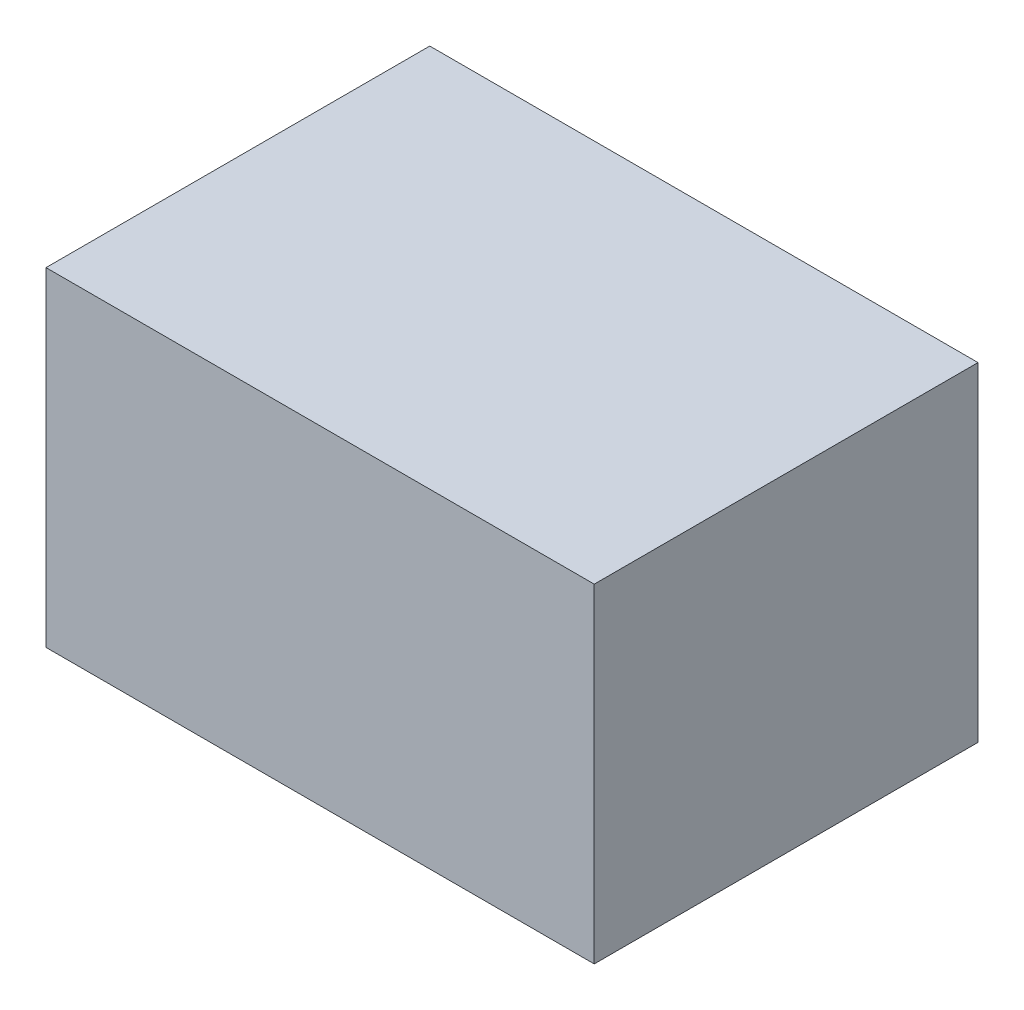
SolidWorks part; units mm, degrees
ref_plane "Спереди" through (0, 0, 0) normal (0, 0, 1) x (1, 0, 0)
ref_plane "Сверху" through (0, 0, 0) normal (0, 1, 0) x (1, 0, 0)
ref_plane "Справа" through (0, 0, 0) normal (1, 0, 0) x (0, 0, -1)
other "Configuration Table"
sketch "Эскиз1" plane through (0, 0, 0) normal (1, 0, 0) x (0, 0, -1)
  line L1 (0, 0) -> (7, 0)
  line L2 (0, 0) -> (0, 6)
  line L3 (0, 6) -> (7, 6)
  line L4 (7, 0) -> (7, 6)
extrude "Бобышка-Вытянуть1" add sketch "Эскиз1" along normal blind 10
